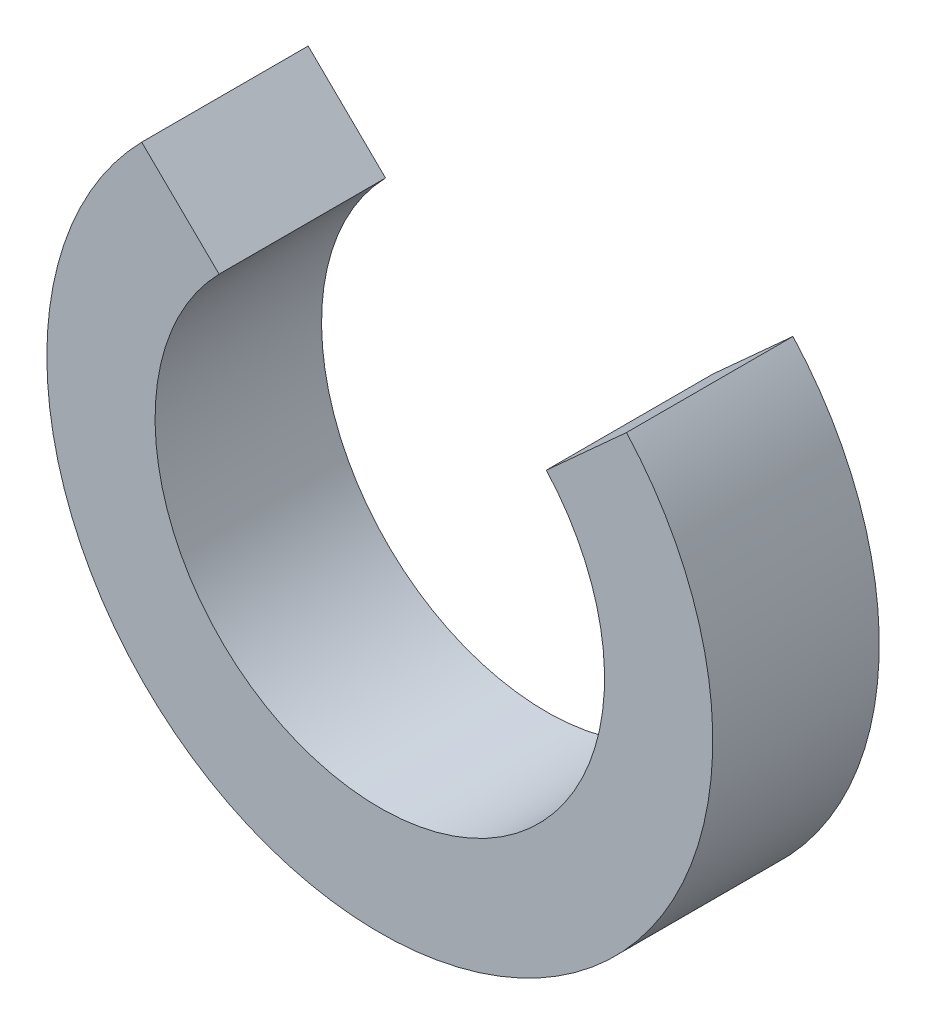
SolidWorks part; units mm, degrees
ref_plane "Front Plane" through (0, 0, 0) normal (0, 0, 1) x (1, 0, 0)
ref_plane "Top Plane" through (0, 0, 0) normal (0, 1, 0) x (1, 0, 0)
ref_plane "Right Plane" through (0, 0, 0) normal (1, 0, 0) x (0, 0, -1)
sketch "Sketch1" plane through (0, 0, 0) normal (0, 0, 1) x (1, 0, 0)
  circle A0 centre (0, 0) radius 27
  circle A1 centre (0, 0) radius 40
extrude "Boss-Extrude1" add sketch "Sketch1" along normal blind 20
sketch "Sketch2" plane through (0, 0, 0) normal (0, 0, 1) x (1, 0, 0)
  line L4 (-19.3093, 18.8719) -> (-28.6064, 27.9584)
  line L5 (20.0034, 18.1346) -> (29.6347, 26.8661)
  circle A0 centre (0, 0) radius 27 construction
  circle A1 centre (0, 0) radius 40 construction
  arc A2 (20.0034, 18.1346) -> (-1.2859, 26.9694) centre (0, 0) ccw
  arc A3 (29.6347, 26.8661) -> (-28.3369, 28.2315) centre (0, 0) cw
  arc A4 (29.6347, 26.8661) -> (-28.6064, 27.9584) centre (0, 0) ccw
extrude "Cut-Extrude4" cut sketch "Sketch2" against normal through all and the other way through all contours A2 L5 A4 L4
